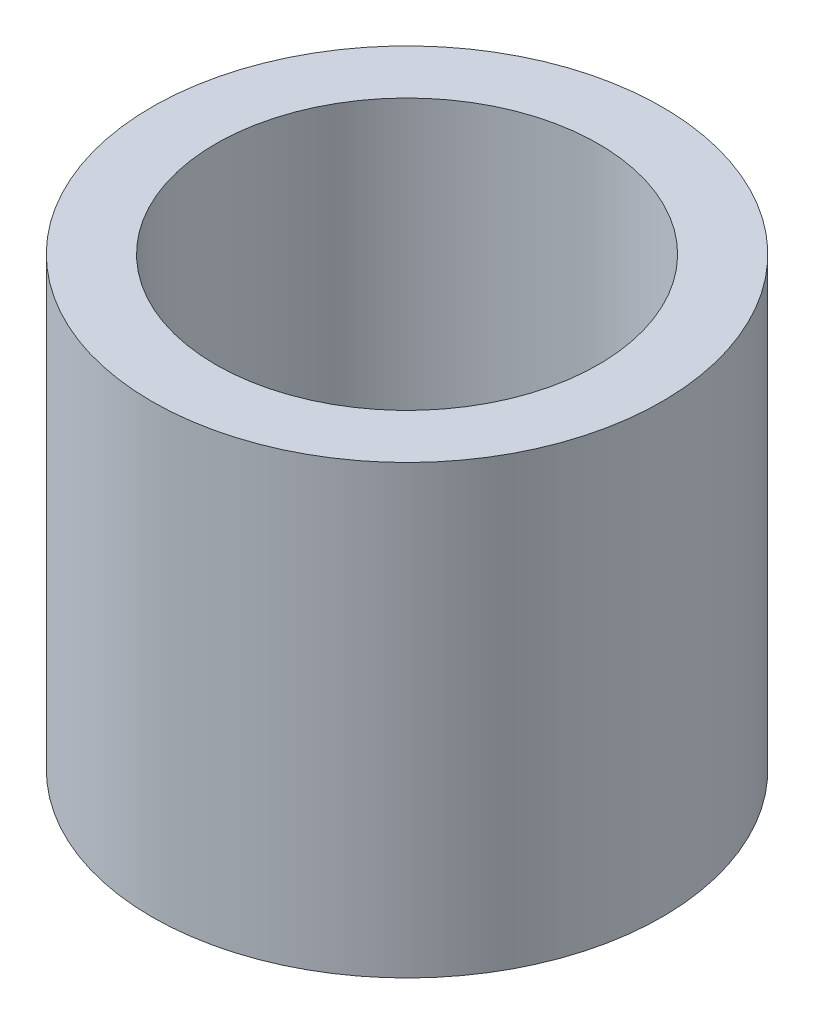
SolidWorks part; units mm, degrees
ref_plane "Front Plane" through (0, 0, 0) normal (0, 0, 1) x (1, 0, 0)
ref_plane "Top Plane" through (0, 0, 0) normal (0, 1, 0) x (1, 0, 0)
ref_plane "Right Plane" through (0, 0, 0) normal (1, 0, 0) x (0, 0, -1)
sketch "Sketch1" plane through (0, 0, 0) normal (0, 1, 0) x (1, 0, 0)
  circle A0 centre (0, 0) radius 1.5
  circle A2 centre (0, 0) radius 2
  dimension "D1" = 3
  dimension "D2" = 4
extrude "Boss-Extrude1" add sketch "Sketch1" along normal blind 3.5
